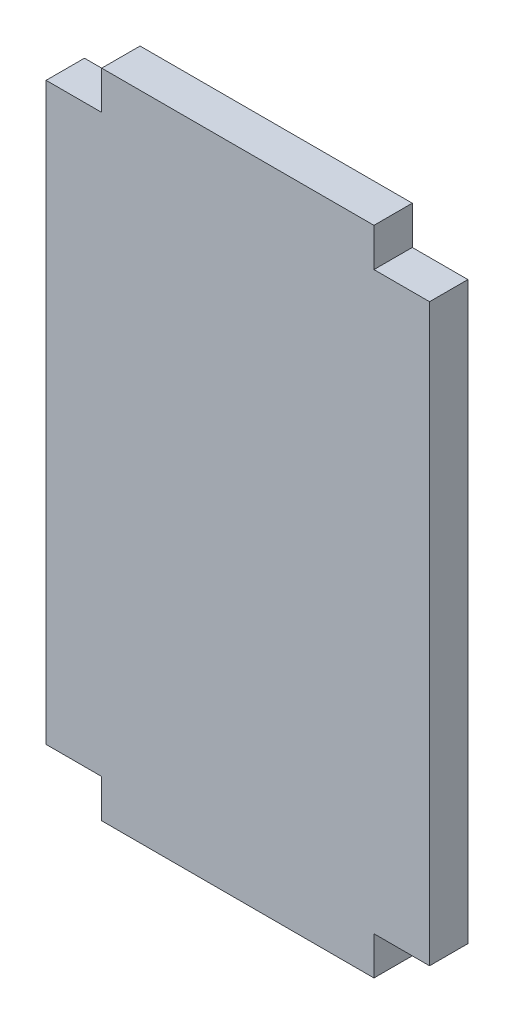
SolidWorks part; units mm, degrees
ref_plane "Front Plane" through (0, 0, 0) normal (0, 0, 1) x (1, 0, 0)
ref_plane "Top Plane" through (0, 0, 0) normal (0, 1, 0) x (1, 0, 0)
ref_plane "Right Plane" through (0, 0, 0) normal (1, 0, 0) x (0, 0, -1)
sketch "Sketch1" plane through (0, 0, 0) normal (0, 0, 1) x (1, 0, 0)
  line L1 (0, 0) -> (-50.8, 0)
  line L2 (0, 0) -> (0, 86.36)
  line L3 (0, 86.36) -> (-50.8, 86.36)
  line L4 (-50.8, 0) -> (-50.8, 86.36)
  dimension "D1" = 86.36
  dimension "D2" = 50.8
extrude "Boss-Extrude1" add sketch "Sketch1" along normal blind 5.08
sketch "Sketch2" plane through (0, 86.36, 0) normal (0, 1, 0) x (1, 0, 0)
  line L0 (0, 0) -> (-7.366, 0) construction
  line L1 (0, 0) -> (-50.8, 0) construction
  line L2 (-7.366, 0) -> (-43.434, 0)
  line L3 (-43.434, 0) -> (-50.8, 0) construction
  line L4 (0, -5.08) -> (-50.8, -5.08) construction
  line L5 (-43.434, 0) -> (-50.8, 0)
  line L6 (-43.434, 0) -> (-43.434, -5.08)
  line L7 (-43.434, -5.08) -> (-50.8, -5.08)
  line L8 (-50.8, 0) -> (-50.8, -5.08)
  line L10 (-7.366, 0) -> (0, 0)
  line L11 (-7.366, 0) -> (-7.366, -5.08)
  line L12 (-7.366, -5.08) -> (0, -5.08)
  line L13 (0, 0) -> (0, -5.08)
  line M4 (0, 0) -> (-50.8, 0)
  line M5 (-50.8, 0) -> (-50.8, -5.08)
  line M6 (-50.8, -5.08) -> (0, -5.08)
  line M7 (0, -5.08) -> (0, 0)
  dimension "D1" = 36.068
extrude "Cut-Extrude1" cut sketch "Sketch2" against normal blind 5.08 contours L6 M4 M5 M6 | L11 M4 M6 M7
sketch "Sketch6" plane through (0, 0, 0) normal (0, -1, 0) x (-1, 0, 0)
  line L0 (50.8, 0) -> (43.435, 0)
  line L1 (50.8, 0) -> (0, 0) construction
  line L2 (43.435, 0) -> (7.365, 0)
  line L3 (7.365, 0) -> (0, 0)
  line L5 (43.435, 0) -> (50.8, 0)
  line L6 (43.435, 0) -> (43.435, -5.08)
  line L7 (43.435, -5.08) -> (50.8, -5.08)
  line L8 (50.8, 0) -> (50.8, -5.08)
  line L9 (7.365, 0) -> (0, 0)
  line L10 (7.365, 0) -> (7.365, -5.08)
  line L11 (7.365, -5.08) -> (0, -5.08)
  line L12 (0, 0) -> (0, -5.08)
  line M4 (50.8, 0) -> (0, 0)
  line M5 (0, 0) -> (0, -5.08)
  line M6 (0, -5.08) -> (50.8, -5.08)
  line M7 (50.8, -5.08) -> (50.8, 0)
  dimension "D1" = 36.07
extrude "Cut-Extrude2" cut sketch "Sketch6" against normal blind 5.08 contours L6 M4 M6 M7 | L10 M4 M5 M6
equation "\"MDFThickness\"= .2in"
equation "\"D1@Boss-Extrude1\"=\"MDFThickness\""
equation "\"D1@Cut-Extrude1\"=\"MDFThickness\""
equation "\"D1@Cut-Extrude2\"=\"MDFThickness\""
